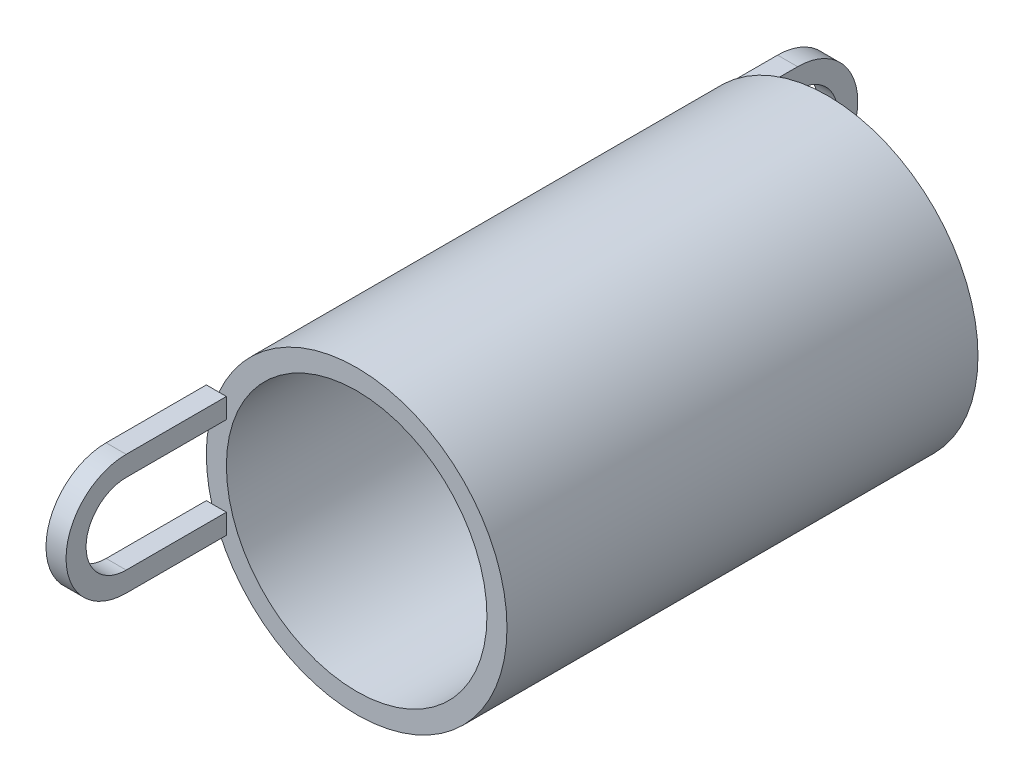
SolidWorks part; units mm, degrees
ref_plane "Plano frontal" through (0, 0, 0) normal (0, 0, 1) x (1, 0, 0)
ref_plane "Plano superior" through (0, 0, 0) normal (0, 1, 0) x (1, 0, 0)
ref_plane "Plano direito" through (0, 0, 0) normal (1, 0, 0) x (0, 0, -1)
sketch "Esboço2" plane through (0, 0, 0) normal (0, 0, 1) x (1, 0, 0)
  circle A0 centre (0, 0) radius 7.5
  circle A1 centre (0, 0) radius 6.5
  point P4 (6.5, 0)
  point P5 (7.5, 0)
  dimension "D2" = 15
  dimension "D1" = 1
extrude "Ressalto-extrusão1" add sketch "Esboço2" along normal blind 23.5
ref_plane "Plano1" through (-7.5, 0, 0) normal (-1, 0, 0) x (0, 0, 1)
sketch "Esboço3" plane through (-7.5, 0, 0) normal (1, 0, 0) x (0, 0, -1)
  line L0 (5, 2) -> (0, 2)
  line L1 (5, 3) -> (0, 3)
  line L2 (0, 3) -> (0, 2)
  line L3 (0, -7.5) -> (0, 7.5) construction
  line L4 (5, 0) -> (0, 0) construction
  line L5 (5, -3) -> (0, -3)
  line L6 (5, -2) -> (0, -2)
  line L7 (0, 0) -> (-23.5, 0) construction
  line L8 (-23.5, 7.5) -> (-23.5, -7.5) construction
  line L9 (-11.75, 0) -> (-11.75, 7.5) construction
  line L10 (0, 7.5) -> (-23.5, 7.5) construction
  line L11 (-28.5, 3) -> (-23.5, 3)
  line L12 (-28.5, 2) -> (-23.5, 2)
  line L13 (-28.5, -2) -> (-23.5, -2)
  line L14 (-28.5, -3) -> (-23.5, -3)
  line L15 (0, -3) -> (0, -2)
  line L16 (-23.5, -3) -> (-23.5, -2)
  line L17 (-23.5, 2) -> (-23.5, 3)
  arc A0 (5, -3) -> (5, 3) centre (5, 0) ccw
  arc A1 (5, -2) -> (5, 2) centre (5, 0) ccw
  arc A2 (-28.5, -2) -> (-28.5, 2) centre (-28.5, 0) cw
  arc A3 (-28.5, -3) -> (-28.5, 3) centre (-28.5, 0) cw
  dimension "D1" = 4
  dimension "D2" = 1
  dimension "D3" = 5
extrude "Ressalto-extrusão2" add sketch "Esboço3" along normal blind 1
